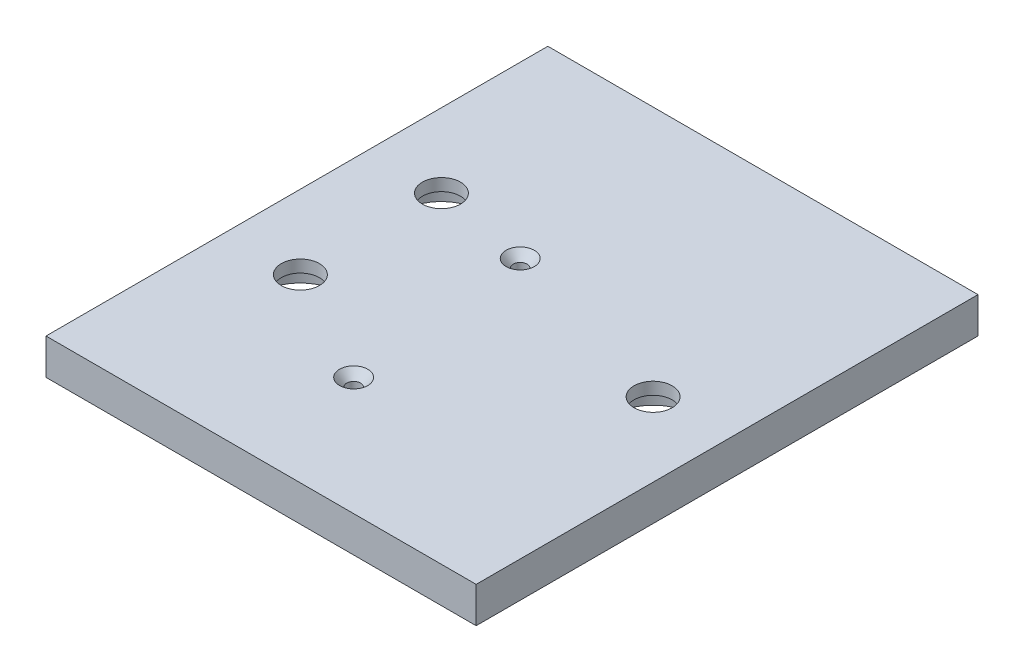
SolidWorks part; units mm, degrees
material "6061-T4 (SS)"
ref_plane "Front Plane" through (0, 0, 0) normal (0, 0, 1) x (1, 0, 0)
ref_plane "Top Plane" through (0, 0, 0) normal (0, 1, 0) x (1, 0, 0)
ref_plane "Right Plane" through (0, 0, 0) normal (1, 0, 0) x (0, 0, -1)
sketch "Sketch1" plane through (0, 0, 0) normal (0, 1, 0) x (1, 0, 0)
  line L1 (0, 0) -> (76.2, 0)
  line L2 (0, 0) -> (0, 88.9)
  line L3 (0, 88.9) -> (76.2, 88.9)
  line L4 (76.2, 0) -> (76.2, 88.9)
  dimension "D1" = 76.2
  dimension "D2" = 88.9
extrude "Boss-Extrude1" add sketch "Sketch1" along normal blind 6.35
hole_wizard "CSK for #2 Flat Head Socket Cap Screw1" positions "Sketch4" profile "Sketch5" countersink size "#2" standard "ANSI Inch"
sketch "Sketch4" plane through (0, 6.35, 0) normal (0, 1, 0) x (1, 0, 0)
  circle A2 centre (33.6, 20.9) radius 0.889 construction
  circle A3 centre (30.1, 53.9) radius 0.889 construction
  point P0 (33.6, 20.9)
  point P2 (30.1, 53.9)
sketch "Sketch5" plane through (33.6, 6.35, -20.9) normal (1, 0, 0) x (0, 0, 1)
  line L0 (0, 0) -> (0, 7.1326)
  line L1 (0, 7.1326) -> (1.2192, 6.4)
  line L2 (1.2192, 6.4) -> (1.2192, 1.4756)
  line L3 (1.2192, 1.4756) -> (2.5019, 0)
  line L5 (2.5019, 0) -> (0, 0)
  line L6 (-1.2192, 1.4756) -> (-2.5019, 0) construction
  line L10 (0, 7.1326) -> (-1.2192, 6.4) construction
  line L11 (0, -6.35) -> (0, 107.95) construction
  dimension "Hole Dia." = 2.4384
  dimension "Hole Depth" = 6.4
  dimension "Near C'Sink Dia." = 5.0038
  dimension "Near C'Sink Angle" = 82
  dimension "Drill Angle" = 118
sketch "Sketch6" plane through (0, 6.35, 0) normal (0, 1, 0) x (1, 0, 0)
  line L0 (30.1, 20.9) -> (30.1, 53.9) construction
  line L1 (30.1, 20.9) -> (33.6, 20.9) construction
  point P4 (30.1, 43.9)
  dimension "D1" = 10
sketch "Sketch7" plane through (0, 0, 0) normal (0, -1, 0) x (1, 0, 0)
  line L0 (38.1, 0) -> (38.1, -88.9) construction
  line L3 (0, 0) -> (76.2, 0) construction
  line L4 (76.2, -88.9) -> (0, -88.9) construction
  point P6 (38.1, -44.45)
hole_wizard "CBORE for 1/4 Binding Head Machine Screw1" positions "Sketch8" profile "Sketch9" counterbore size "1/4" standard "ANSI Inch"
sketch "Sketch8" plane through (0, 0, 0) normal (0, -1, 0) x (-1, 0, 0)
  circle A0 centre (-13.1064, 31.9532) radius 3.302 construction
  circle A1 centre (-13.1064, 56.9468) radius 3.302 construction
  circle A2 centre (-63.0936, 44.45) radius 3.302 construction
  point P0 (-63.0936, 44.45)
  point P2 (-13.1064, 31.9532)
  point P4 (-13.1064, 56.9468)
sketch "Sketch9" plane through (63.0936, 0, -44.45) normal (1, 0, 0) x (0, 0, -1)
  line L0 (0, 0) -> (0, 8.4298)
  line L1 (0, 8.4298) -> (3.3782, 6.4)
  line L2 (3.3782, 6.4) -> (3.3782, 4.191)
  line L3 (3.3782, 4.191) -> (7.1437, 4.191)
  line L4 (7.1437, 4.191) -> (7.1437, 0)
  line L5 (7.1437, 0) -> (0, 0)
  line L10 (0, 8.4298) -> (-3.3782, 6.4) construction
  line L11 (0, -6.35) -> (0, 107.95) construction
  dimension "Hole Dia." = 6.7564
  dimension "Hole Depth" = 6.4
  dimension "C'Bore Dia." = 14.2875
  dimension "C'Bore Depth" = 4.191
  dimension "Drill Angle" = 118
